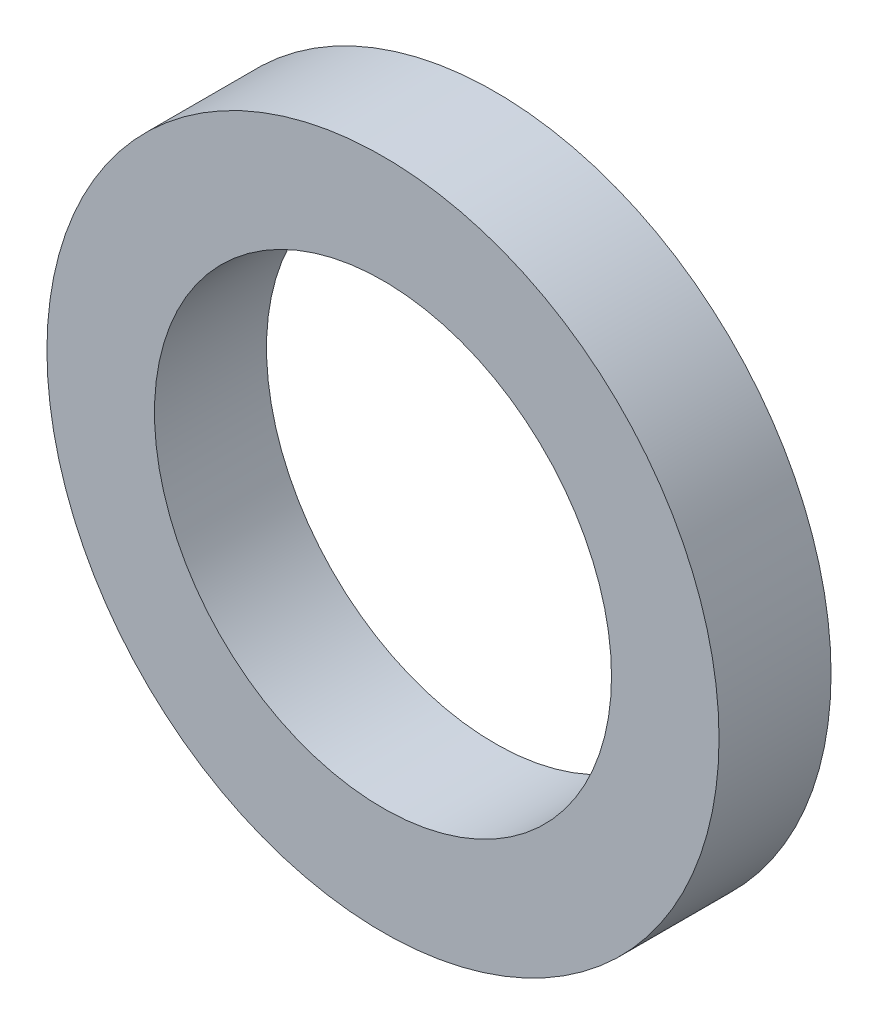
SolidWorks part; units mm, degrees
material "Copper"
ref_plane "Front Plane" through (0, 0, 0) normal (0, 0, 1) x (1, 0, 0)
ref_plane "Top Plane" through (0, 0, 0) normal (0, 1, 0) x (1, 0, 0)
ref_plane "Right Plane" through (0, 0, 0) normal (1, 0, 0) x (0, 0, -1)
sketch "Sketch1" plane through (0, 0, 0) normal (0, 0, 1) x (1, 0, 0)
  circle A0 centre (0, 0) radius 9.525
  circle A1 centre (0, 0) radius 6.477
  dimension "D1" = 19.05
  dimension "D2" = 12.954
extrude "Boss-Extrude1" add sketch "Sketch1" along normal blind 3.175
